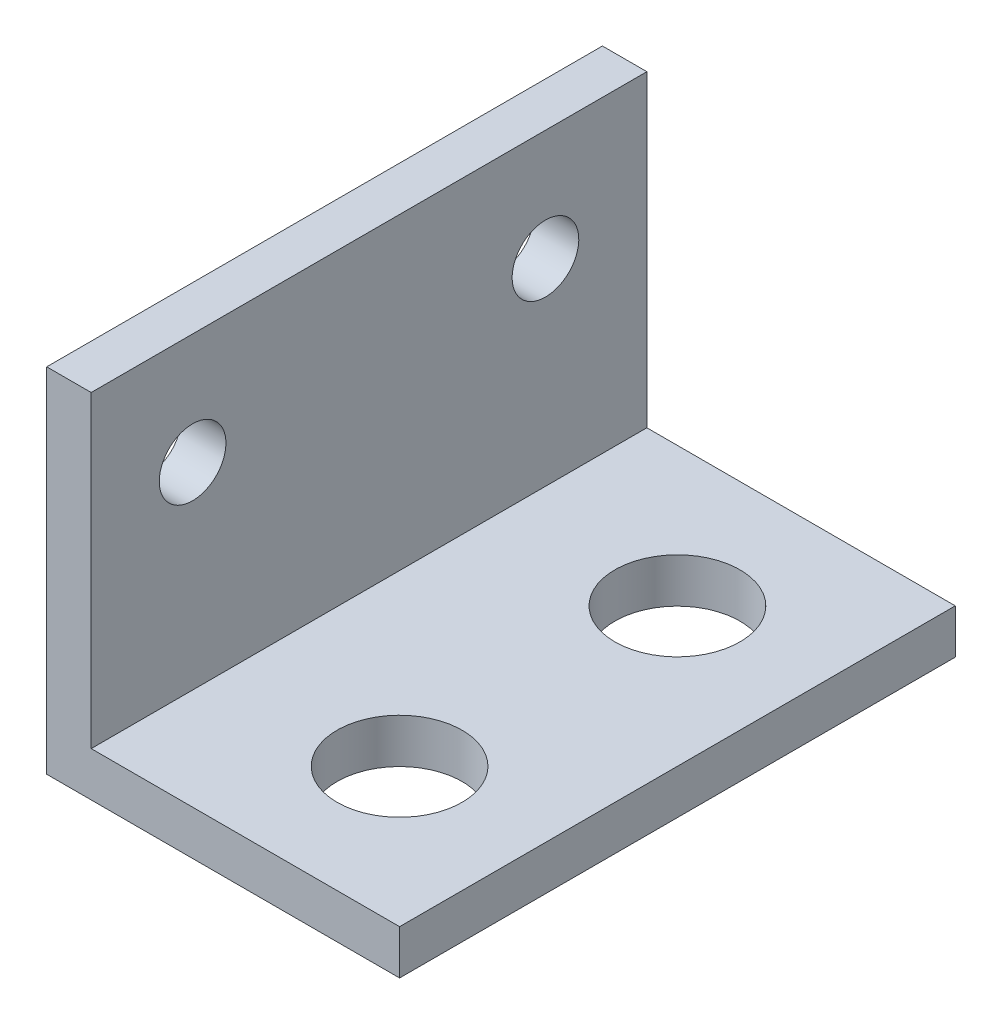
SolidWorks part; units mm, degrees
material "6061-T6 (SS)"
ref_plane "Front Plane" through (0, 0, 0) normal (0, 0, 1) x (1, 0, 0)
ref_plane "Top Plane" through (0, 0, 0) normal (0, 1, 0) x (1, 0, 0)
ref_plane "Right Plane" through (0, 0, 0) normal (1, 0, 0) x (0, 0, -1)
sketch "Sketch1" plane through (0, 0, 0) normal (0, 0, 1) x (1, 0, 0)
  line L0 (0, 0) -> (0, 12.7)
  line L1 (0, 12.7) -> (1.6002, 12.7)
  line L2 (1.6002, 12.7) -> (1.6002, 1.6002)
  line L3 (1.6002, 1.6002) -> (12.7, 1.6002)
  line L4 (12.7, 1.6002) -> (12.7, 0)
  line L5 (12.7, 0) -> (0, 0)
  dimension "D1" = 12.7
  dimension "D2" = 12.7
  dimension "D3" = 1.6002
  dimension "D4" = 1.6002
extrude "Boss-Extrude1" add sketch "Sketch1" along normal mid plane 20 contours L0 L1 L2 L3 L4 L5
sketch "Sketch4" plane through (0, 1.6002, 0) normal (0, 1, 0) x (1, 0, 0)
  line L0 (12.7, -10) -> (12.7, 10) construction
  line L1 (1.6002, -10) -> (12.7, -10) construction
  line L2 (1.6002, 10) -> (12.7, 10) construction
  point P0 (7.7, -5)
  point P2 (7.7, 5)
  point P7 (0, 0)
  dimension "D1" = 5
  dimension "D2" = 5
  dimension "D3" = 5
hole_wizard "M4 Clearance Hole1" positions "Sketch4" profile "Sketch3" hole size "M4" standard "ANSI Metric" end condition through all
sketch "Sketch3" plane through (7.7, 1.6002, 5) normal (1, 0, 0) x (0, 0, 1)
  line L0 (0, 0) -> (0, 1.6002)
  line L1 (0, 1.6002) -> (2.25, 1.6002)
  line L2 (2.25, 1.6002) -> (2.25, 0)
  line L5 (2.25, 0) -> (0, 0)
  line L11 (0, -6.35) -> (0, 107.95) construction
  dimension "Thru Hole Dia." = 4.5
  dimension "Thru Hole Depth" = 1.6002
sketch "Sketch7" plane through (0, 0, 0) normal (-1, 0, 0) x (0, 0, 1)
  line L0 (10, 12.7) -> (-10, 12.7) construction
  point P0 (-6.35, 8.7)
  point P2 (6.35, 8.7)
  dimension "D1" = 4
  dimension "D2" = 12.7
  dimension "D3" = 6.35
hole_wizard "M2 Clearance Hole1" positions "Sketch7" profile "Sketch6" hole size "M2" standard "ANSI Metric" end condition through all
sketch "Sketch6" plane through (0, 8.7, -6.35) normal (0, 1, 0) x (0, 0, 1)
  line L0 (0, 0) -> (0, 12.7)
  line L1 (0, 12.7) -> (1.2, 12.7)
  line L2 (1.2, 12.7) -> (1.2, 0)
  line L5 (1.2, 0) -> (0, 0)
  line L11 (0, -6.35) -> (0, 107.95) construction
  dimension "Thru Hole Dia." = 2.4
  dimension "Thru Hole Depth" = 12.7
